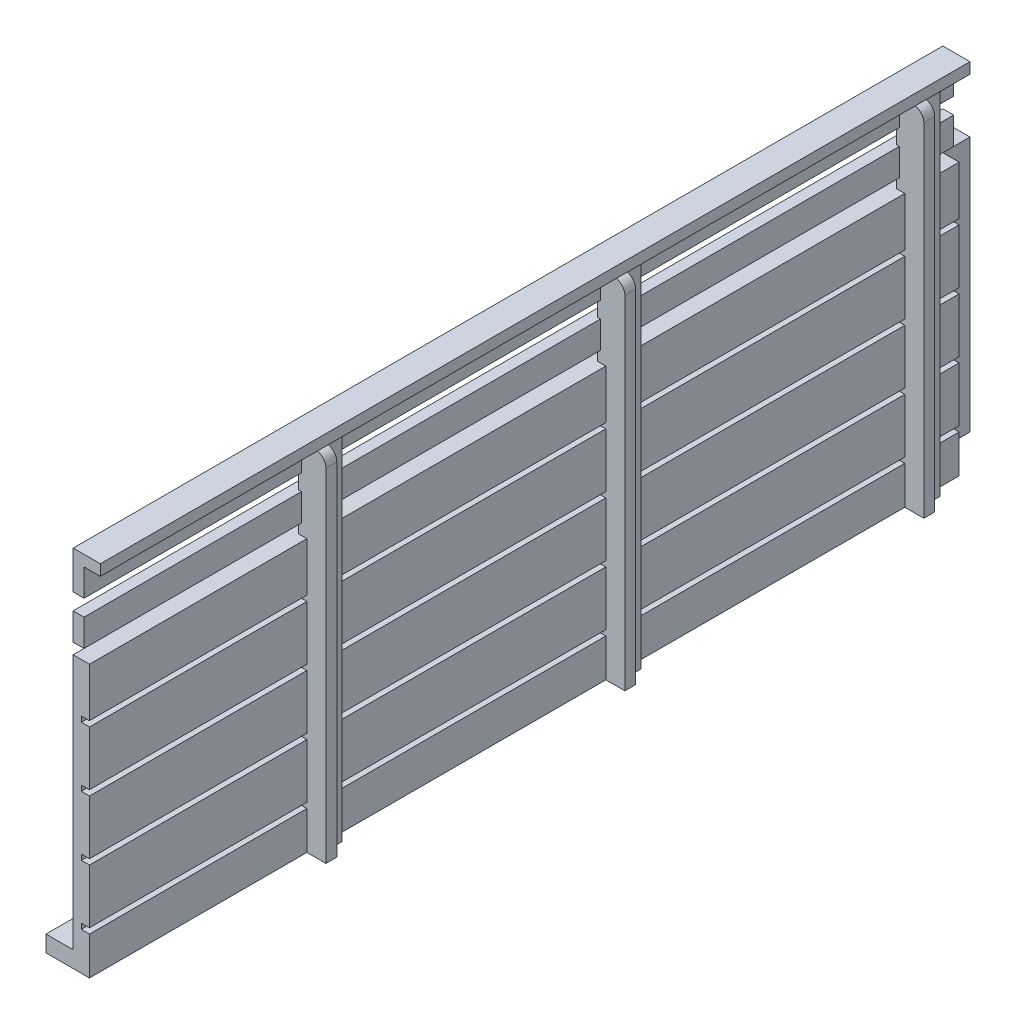
SolidWorks part; units mm, degrees
ref_plane "Front Plane" through (0, 0, 0) normal (0, 0, 1) x (1, 0, 0)
ref_plane "Top Plane" through (0, 0, 0) normal (0, 1, 0) x (1, 0, 0)
ref_plane "Right Plane" through (0, 0, 0) normal (1, 0, 0) x (0, 0, -1)
sketch "Sketch1" plane through (0, 0, 0) normal (1, 0, 0) x (0, 0, -1)
  line L1 (-80, 25) -> (80, 25)
  line L2 (-80, 25) -> (-80, -25)
  line L3 (-80, -25) -> (80, -25)
  line L4 (80, 25) -> (80, -25)
  line L5 (-80, 25) -> (80, -25) construction
  line L6 (-80, -25) -> (80, 25) construction
  point P0 (0, 0)
  dimension "D1" = 50
  dimension "D2" = 160
extrude "Boss-Extrude1" add sketch "Sketch1" along normal blind 3
sketch "Sketch3" plane through (3, 0, 0) normal (1, 0, 0) x (0, 0, -1)
  line L0 (-80, 25) -> (-80, -25) construction
  line L1 (-80, -17) -> (80, -17)
  line L2 (-80, -17) -> (-80, -18)
  line L3 (-80, -18) -> (80, -18)
  line L4 (80, -17) -> (80, -18)
  line L5 (80, -25) -> (80, 25) construction
  line L6 (-80, -25) -> (80, -25) construction
  line L7 (80, 25) -> (-80, 25) construction
  line L8 (-80, -6) -> (80, -6)
  line L9 (-80, -6) -> (-80, -7)
  line L10 (-80, -7) -> (80, -7)
  line L11 (80, -6) -> (80, -7)
  line L12 (-80, 5) -> (80, 5)
  line L13 (-80, 5) -> (-80, 4)
  line L14 (-80, 4) -> (80, 4)
  line L15 (80, 5) -> (80, 4)
  line L16 (-80, 16) -> (80, 16)
  line L17 (-80, 16) -> (-80, 15)
  line L18 (-80, 15) -> (80, 15)
  line L19 (80, 16) -> (80, 15)
  dimension "D1" = 1
  dimension "D2" = 7
  dimension "D3" = 1
  dimension "D4" = 10
  dimension "D5" = 1
  dimension "D6" = 10
  dimension "D7" = 1
  dimension "D8" = 10
  dimension "D9" = 9
extrude "Cut-Extrude1" cut sketch "Sketch3" against normal blind 1.5
sketch "Sketch4" plane through (3, 0, 0) normal (1, 0, 0) x (0, 0, -1)
  line L0 (-80, -25) -> (80, -25) construction
  line L1 (-40, -25) -> (-35, -25)
  line L2 (-40, -25) -> (-40, 40)
  line L3 (-40, 40) -> (-35, 40)
  line L4 (-35, -25) -> (-35, 40)
  line L5 (-80, -7) -> (-80, -17) construction
  line L7 (15, -25) -> (20, -25)
  line L8 (15, -25) -> (15, 40)
  line L9 (15, 40) -> (20, 40)
  line L10 (20, -25) -> (20, 40)
  line L11 (70, -25) -> (75, -25)
  line L12 (70, -25) -> (70, 40)
  line L13 (70, 40) -> (75, 40)
  line L14 (75, -25) -> (75, 40)
  dimension "D1" = 65
  dimension "D2" = 5
  dimension "D3" = 40
  dimension "D4" = 5
  dimension "D5" = 65
  dimension "D6" = 50
  dimension "D7" = 5
  dimension "D8" = 50
  dimension "D9" = 65
extrude "Boss-Extrude2" add sketch "Sketch4" along normal mid plane 3
sketch "Sketch5" plane through (4.5, 0, 0) normal (1, 0, 0) x (0, 0, -1)
  line L0 (-35, 40) -> (-40, 40) construction
  line L1 (-40, -25) -> (-38, -25)
  line L2 (-40, -25) -> (-40, 40)
  line L3 (-40, 40) -> (-38, 40)
  line L4 (-38, -25) -> (-38, 40)
  line L5 (20, 40) -> (15, 40) construction
  line L6 (15, -25) -> (17, -25)
  line L7 (15, -25) -> (15, 40)
  line L8 (15, 40) -> (17, 40)
  line L9 (17, -25) -> (17, 40)
  line L10 (75, 40) -> (70, 40) construction
  line L11 (70, -25) -> (72, -25)
  line L12 (70, -25) -> (70, 40)
  line L13 (70, 40) -> (72, 40)
  line L14 (72, -25) -> (72, 40)
  dimension "D1" = 2
  dimension "D2" = 65
  dimension "D3" = 2
  dimension "D4" = 65
  dimension "D5" = 2
extrude "Boss-Extrude3" add sketch "Sketch5" along normal blind 2
fillet "Fillet1" radius 2 3 edges at (6.5, 40, -71) (6.5, 40, -16) (6.5, 40, 39)
sketch "Sketch6" plane through (0, 40, 0) normal (0, 1, 0) x (1, 0, 0)
  line L0 (3, 80) -> (0, 80) construction
  line L1 (0, -80) -> (5, -80)
  line L2 (0, -80) -> (0, 80)
  line L3 (0, 80) -> (5, 80)
  line L4 (5, -80) -> (5, 80)
  dimension "D2" = 5
sketch "Sketch8" plane through (0, 0, 0) normal (-1, 0, 0) x (0, 0, 1)
  line L0 (80, -25) -> (80, 40) construction
  line L1 (80, 40) -> (-80, 40) construction
  line L2 (-80, 25) -> (80, 25) construction
  line L3 (80, 27) -> (-80, 27)
  line L4 (80, 27) -> (80, 32)
  line L5 (80, 32) -> (-80, 32)
  line L6 (-80, 27) -> (-80, 32)
  line L7 (-80, -25) -> (-80, 25) construction
  line L8 (80, 35) -> (-80, 35)
  line L9 (80, 35) -> (80, 40)
  line L10 (80, 40) -> (-80, 40)
  line L11 (-80, 35) -> (-80, 40)
  dimension "D1" = 5
  dimension "D2" = 2
  dimension "D4" = 5
  dimension "D5" = 3
extrude "Boss-Extrude4" add sketch "Sketch8" against normal blind 2
extrude "Boss-Extrude5" add sketch "Sketch6" along normal blind 2
sketch "Sketch10" plane through (0, 0, 0) normal (-1, 0, 0) x (0, 0, 1)
  line L0 (80, 25) -> (80, -25) construction
  line L1 (-80, -25) -> (80, -25)
  line L2 (-80, -25) -> (-80, -22)
  line L3 (-80, -22) -> (80, -22)
  line L4 (80, -25) -> (80, -22)
  dimension "D1" = 3
extrude "Boss-Extrude6" add sketch "Sketch10" along normal blind 5
sketch "Sketch13" plane through (0, 0, 0) normal (-1, 0, 0) x (0, 0, 1)
  line L0 (-80, 25) -> (80, 25) construction
  line L1 (-75, 25) -> (-85, 25)
  line L2 (-75, 25) -> (-75, -22.0074)
  line L3 (-75, -22.0074) -> (-85, -22.0074)
  line L4 (-85, 25) -> (-85, -22.0074)
  point P8 (-78.0402, 25.7804)
  dimension "D1" = 10
  dimension "D2" = 5
extrude "Boss-Extrude7" add sketch "Sketch13" along normal up to surface (5 mm away) up to face at (-5, -23.5, 0)
